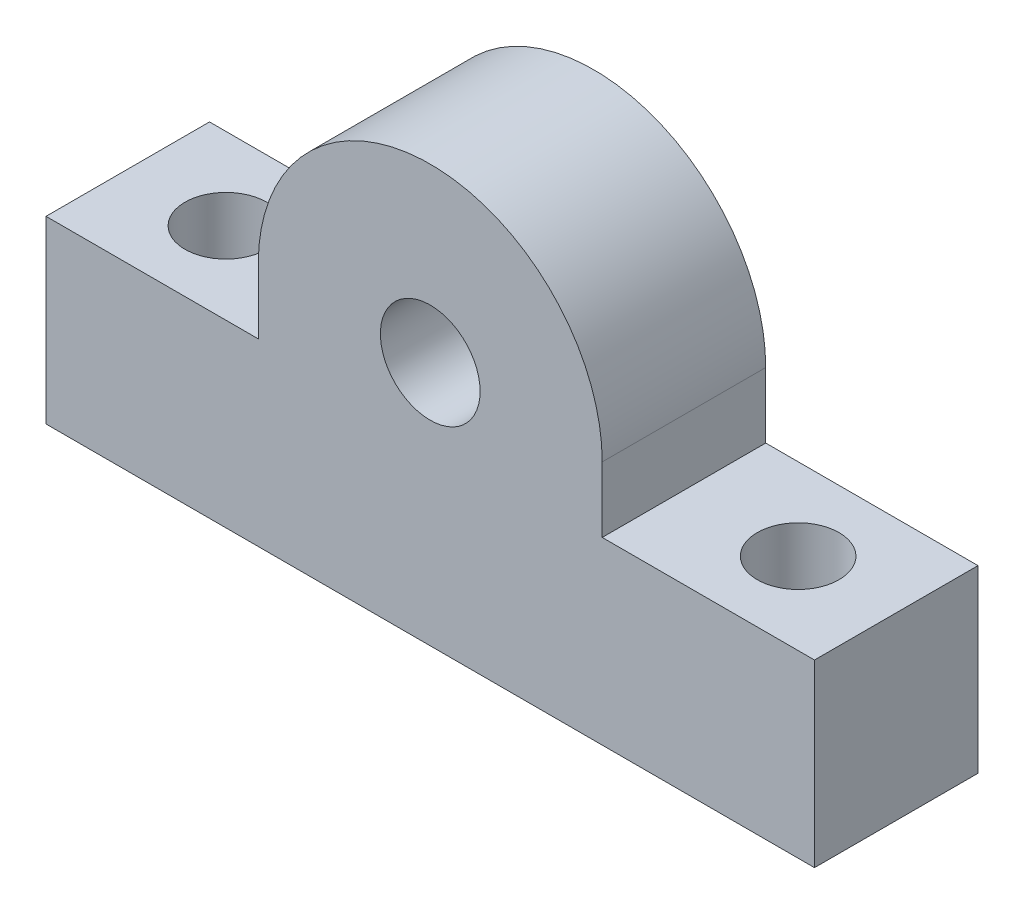
SolidWorks part; units mm, degrees
ref_plane "Front Plane" through (0, 0, 0) normal (0, 0, 1) x (1, 0, 0)
ref_plane "Top Plane" through (0, 0, 0) normal (0, 1, 0) x (1, 0, 0)
ref_plane "Right Plane" through (0, 0, 0) normal (1, 0, 0) x (0, 0, -1)
sketch "Sketch1" plane through (0, 0, 0) normal (0, 0, 1) x (1, 0, 0)
  line L1 (-23.5, 5.5) -> (23.5, 5.5)
  line L2 (-23.5, 5.5) -> (-23.5, -5.5)
  line L3 (-23.5, -5.5) -> (23.5, -5.5)
  line L4 (23.5, 5.5) -> (23.5, -5.5)
  line L5 (-23.5, 5.5) -> (23.5, -5.5) construction
  line L6 (-23.5, -5.5) -> (23.5, 5.5) construction
  point P0 (0, 0)
  dimension "D1" = 47
  dimension "D2" = 11
extrude "Boss-Extrude1" add sketch "Sketch1" along normal blind 10
sketch "Sketch3" plane through (0, -5.5, 0) normal (0, -1, 0) x (1, 0, 0)
  line L0 (0, 10) -> (0, 0) construction
  line L1 (-23.5, 10) -> (23.5, 10) construction
  line L2 (-23.5, 0) -> (23.5, 0) construction
  line L3 (-23.5, 5) -> (23.5, 5) construction
  line L4 (-23.5, 10) -> (-23.5, 0) construction
  line L5 (23.5, 10) -> (23.5, 0) construction
  line L6 (0, 5) -> (-23.5, 5)
  line L7 (-23.5, 5) -> (-17.5, 5)
  circle A0 centre (-17.5, 5) radius 2.5
  circle A1 centre (17.5, 5) radius 2.5
extrude "Cut-Extrude1" cut sketch "Sketch3" against normal up to next contours L6 A0 | L6 A0 | A1
sketch "Sketch4" plane through (0, 0, 10) normal (0, 0, 1) x (1, 0, 0)
  line L0 (0, -5.5) -> (0, 9.5)
  line L1 (-23.5, -5.5) -> (23.5, -5.5) construction
  line L2 (0, 9.5) -> (0, 2) construction
  line L3 (10.5174, 9.5) -> (10.5174, 2)
  line L4 (-10.5174, 9.5) -> (-10.5174, 2)
  circle A0 centre (0, 9.5) radius 3.05
  arc A1 (10.5174, 9.5) -> (-10.5174, 9.5) centre (0, 9.5) ccw
  arc A2 (-10.5174, 2) -> (10.5174, 2) centre (0, 2) ccw
  point P6 (0, 5.75)
extrude "Boss-Extrude3" add sketch "Sketch4" against normal blind 10
